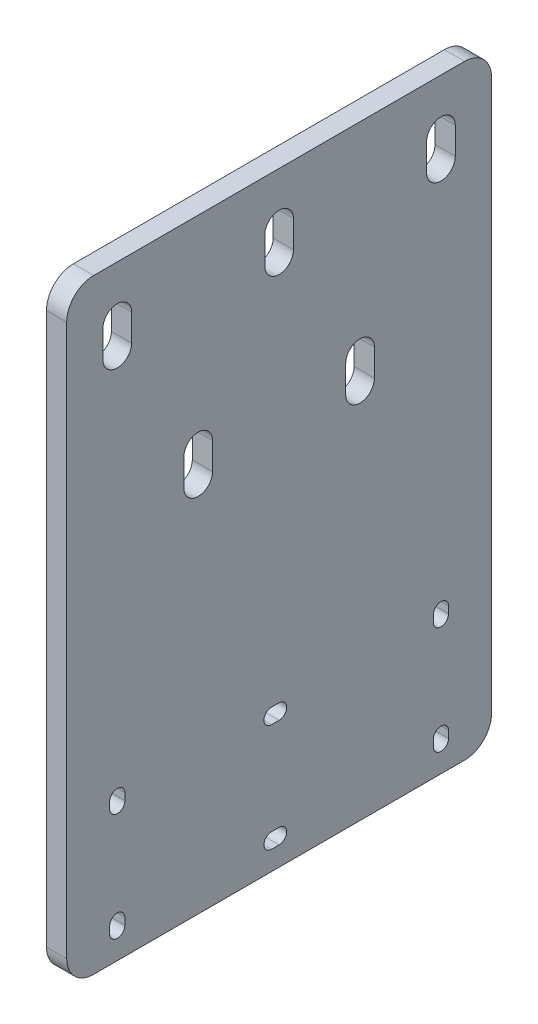
SolidWorks part; units mm, degrees
ref_plane "前视基准面" through (0, 0, 0) normal (0, 0, 1) x (1, 0, 0)
ref_plane "上视基准面" through (0, 0, 0) normal (0, 1, 0) x (1, 0, 0)
ref_plane "右视基准面" through (0, 0, 0) normal (1, 0, 0) x (0, 0, -1)
sketch "草图1" plane through (0, 0, 0) normal (1, 0, 0) x (0, 0, -1)
  line L0 (12.75, 10) -> (12.75, 8)
  line L5 (8, 0) -> (118, 0)
  line L6 (0, 8) -> (0, 171.5)
  line L7 (8, 179.5) -> (118, 179.5)
  line L8 (126, 8) -> (126, 171.5)
  line L9 (12.75, 42) -> (12.75, 40)
  line L10 (17.25, 8) -> (17.25, 10)
  line L11 (17.25, 40) -> (17.25, 42)
  line L12 (108.75, 42) -> (108.75, 40)
  line L13 (113.25, 40) -> (113.25, 42)
  line L14 (108.75, 10) -> (108.75, 8)
  line L15 (113.25, 8) -> (113.25, 10)
  line L20 (60.75, 37.75) -> (63, 37.75)
  line L21 (60.75, 42.25) -> (63, 42.25)
  line L22 (60.75, 10.25) -> (63, 10.25)
  line L23 (60.75, 5.75) -> (63, 5.75)
  line L24 (39, 118) -> (39, 105.6258) construction
  line L25 (39, 118) -> (39, 84.4795) construction
  line L26 (34.75, 116.5) -> (34.75, 119.5)
  line L27 (43.25, 119.5) -> (43.25, 116.5)
  line L28 (82.75, 116.5) -> (82.75, 119.5)
  line L29 (91.25, 119.5) -> (91.25, 116.5)
  line L30 (-33.9112, 163) -> (146.7607, 163) construction
  line L31 (15, 40) -> (15, 140) construction
  line L32 (10.75, 164.5) -> (10.75, 161.5)
  line L33 (19.25, 164.5) -> (19.25, 161.5)
  line L34 (67.25, 164.5) -> (67.25, 161.5)
  line L35 (58.75, 164.5) -> (58.75, 161.5)
  line L36 (115.25, 164.5) -> (115.25, 161.5)
  line L37 (106.75, 164.5) -> (106.75, 161.5)
  arc A0 (12.75, 8) -> (17.25, 8) centre (15, 8) ccw
  arc A1 (17.25, 10) -> (12.75, 10) centre (15, 10) ccw
  arc A2 (17.25, 42) -> (12.75, 42) centre (15, 42) ccw
  arc A3 (12.75, 40) -> (17.25, 40) centre (15, 40) ccw
  arc A4 (113.25, 42) -> (108.75, 42) centre (111, 42) ccw
  arc A5 (108.75, 40) -> (113.25, 40) centre (111, 40) ccw
  arc A6 (113.25, 10) -> (108.75, 10) centre (111, 10) ccw
  arc A7 (108.75, 8) -> (113.25, 8) centre (111, 8) ccw
  arc A12 (60.75, 10.25) -> (60.75, 5.75) centre (60.75, 8) ccw
  arc A14 (63, 37.75) -> (63, 42.25) centre (63, 40) ccw
  arc A15 (60.75, 42.25) -> (60.75, 37.75) centre (60.75, 40) ccw
  arc A16 (63, 5.75) -> (63, 10.25) centre (63, 8) ccw
  circle A17 centre (39, 118) radius 4.25 construction
  arc A20 (43.25, 119.5) -> (34.75, 119.5) centre (39, 119.5) ccw
  arc A21 (34.75, 116.5) -> (43.25, 116.5) centre (39, 116.5) ccw
  arc A22 (82.75, 116.5) -> (91.25, 116.5) centre (87, 116.5) ccw
  arc A23 (91.25, 119.5) -> (82.75, 119.5) centre (87, 119.5) ccw
  arc A24 (10.75, 161.5) -> (19.25, 161.5) centre (15, 161.5) ccw
  arc A25 (19.25, 164.5) -> (10.75, 164.5) centre (15, 164.5) ccw
  arc A26 (67.25, 164.5) -> (58.75, 164.5) centre (63, 164.5) ccw
  arc A27 (58.75, 161.5) -> (67.25, 161.5) centre (63, 161.5) ccw
  arc A28 (115.25, 164.5) -> (106.75, 164.5) centre (111, 164.5) ccw
  arc A29 (106.75, 161.5) -> (115.25, 161.5) centre (111, 161.5) ccw
  arc A30 (8, 0) -> (0, 8) centre (8, 8) cw
  arc A31 (118, 0) -> (126, 8) centre (118, 8) ccw
  arc A32 (118, 179.5) -> (126, 171.5) centre (118, 171.5) cw
  arc A33 (0, 171.5) -> (8, 179.5) centre (8, 171.5) cw
  point P81 (0, 0)
  dimension "D1" = 4.5
  dimension "D6" = 2
  dimension "D9" = 8.5
  dimension "D10" = 118
  dimension "D11" = 8.5
  dimension "D12" = 8.5
  dimension "D17" = 8.5
  dimension "D18" = 8.5
  dimension "D22" = 8
  dimension "D3" = 15
  dimension "D4" = 8
  dimension "D8" = 24
  dimension "D7" = 15
  dimension "D13" = 1.5
  dimension "D14" = 1.5
  dimension "D15" = 45
  dimension "D19" = 1.5
  dimension "D20" = 1.5
  dimension "D21" = 15
  dimension "D2" = 2
  dimension "D5" = 2
  dimension "D16" = 2
extrude "凸台-拉伸2" add sketch "草图1" along normal blind 6
sketch "草图2" plane through (0, 0, 0) normal (1, 0, 0) x (0, 0, -1)
  line L0 (39, 119.5) -> (39, 111.5) construction
  line L1 (43.25, 119.5) -> (43.25, 111.5)
  line L2 (34.75, 119.5) -> (34.75, 111.5)
  line L3 (39, 111.5) -> (105.327, 111.5) construction
  line L4 (87, 119.5) -> (87, 111.5) construction
  line L5 (91.25, 119.5) -> (91.25, 111.5)
  line L6 (82.75, 119.5) -> (82.75, 111.5)
  line L7 (15, 164.5) -> (118.7893, 164.5) construction
  line L8 (118.7893, 164.5) -> (118.7893, 156.5) construction
  line L9 (118.7893, 156.5) -> (15, 156.5) construction
  line L10 (15, 164.5) -> (15, 156.5) construction
  line L11 (19.25, 164.5) -> (19.25, 156.5)
  line L12 (10.75, 164.5) -> (10.75, 156.5)
  line L13 (63, 164.5) -> (63, 156.5) construction
  line L14 (67.25, 164.5) -> (67.25, 156.5)
  line L15 (58.75, 164.5) -> (58.75, 156.5)
  line L16 (111, 164.5) -> (111, 156.5) construction
  line L17 (115.25, 164.5) -> (115.25, 156.5)
  line L18 (106.75, 164.5) -> (106.75, 156.5)
  arc A0 (43.25, 119.5) -> (34.75, 119.5) centre (39, 119.5) ccw construction
  arc A1 (43.25, 119.5) -> (34.75, 119.5) centre (39, 119.5) ccw construction
  arc A3 (43.25, 119.5) -> (34.75, 119.5) centre (39, 119.5) ccw
  arc A4 (34.75, 111.5) -> (43.25, 111.5) centre (39, 111.5) ccw
  arc A5 (91.25, 119.5) -> (82.75, 119.5) centre (87, 119.5) ccw construction
  arc A6 (91.25, 119.5) -> (82.75, 119.5) centre (87, 119.5) ccw construction
  arc A7 (91.25, 119.5) -> (82.75, 119.5) centre (87, 119.5) ccw
  arc A8 (82.75, 111.5) -> (91.25, 111.5) centre (87, 111.5) ccw
  arc A9 (19.25, 164.5) -> (10.75, 164.5) centre (15, 164.5) ccw construction
  arc A10 (19.25, 164.5) -> (10.75, 164.5) centre (15, 164.5) ccw construction
  arc A11 (19.25, 164.5) -> (10.75, 164.5) centre (15, 164.5) ccw
  arc A12 (10.75, 156.5) -> (19.25, 156.5) centre (15, 156.5) ccw
  arc A13 (67.25, 164.5) -> (58.75, 164.5) centre (63, 164.5) ccw construction
  arc A14 (67.25, 164.5) -> (58.75, 164.5) centre (63, 164.5) ccw construction
  arc A15 (115.25, 164.5) -> (106.75, 164.5) centre (111, 164.5) ccw construction
  arc A16 (115.25, 164.5) -> (106.75, 164.5) centre (111, 164.5) ccw construction
  arc A17 (67.25, 164.5) -> (58.75, 164.5) centre (63, 164.5) ccw
  arc A18 (58.75, 156.5) -> (67.25, 156.5) centre (63, 156.5) ccw
  arc A19 (115.25, 164.5) -> (106.75, 164.5) centre (111, 164.5) ccw
  arc A20 (106.75, 156.5) -> (115.25, 156.5) centre (111, 156.5) ccw
  point P3 (39, 115.5)
  point P14 (87, 115.5)
  point P26 (15, 160.5)
  point P37 (63, 160.5)
  point P43 (111, 160.5)
  dimension "D1" = 8
  dimension "D2" = 8
extrude "切除-拉伸1" cut sketch "草图2" against normal through all both and the other way through all
